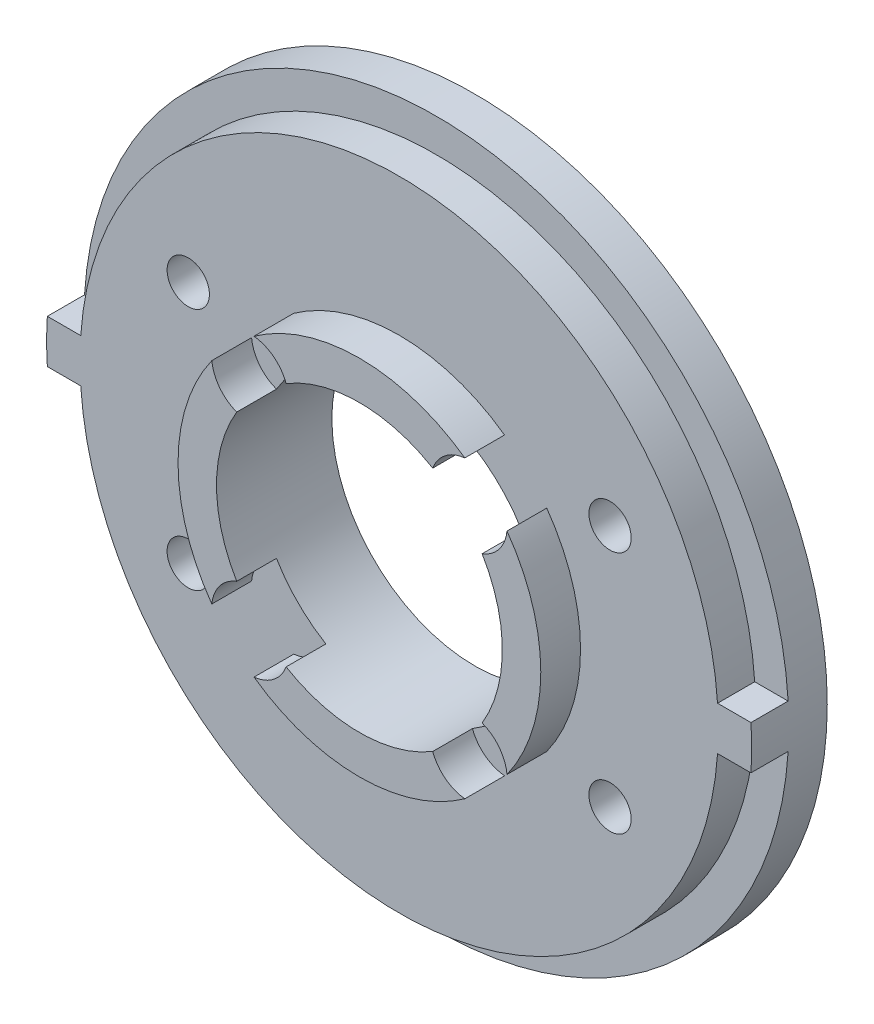
SolidWorks part; units mm, degrees
ref_plane "Front Plane" through (0, 0, 0) normal (0, 0, 1) x (1, 0, 0)
ref_plane "Top Plane" through (0, 0, 0) normal (0, 1, 0) x (1, 0, 0)
ref_plane "Right Plane" through (0, 0, 0) normal (1, 0, 0) x (0, 0, -1)
sketch "Sketch1" plane through (0, 0, 0) normal (0, 0, 1) x (1, 0, 0)
  circle A0 centre (0, 0) radius 11.15
  circle A1 centre (0, 0) radius 27.5
  dimension "D1" = 22.3
  dimension "D2" = 55
extrude "Boss-Extrude1" add sketch "Sketch1" along normal blind 9
sketch "Sketch2" plane through (0, 0, 0) normal (0, 0, 1) x (1, 0, 0)
  line L0 (-27.4474, 1.7) -> (-24.8402, 1.7)
  line L1 (-32.4957, 1.7) -> (38.4812, 1.7) construction
  line L2 (-32.4957, 1.7) -> (-32.4957, -1.7) construction
  line L3 (-32.4957, -1.7) -> (38.4812, -1.7) construction
  line L4 (38.4812, 1.7) -> (38.4812, -1.7) construction
  line L5 (24.8402, 1.7) -> (27.4474, 1.7)
  line L6 (27.4474, -1.7) -> (24.8419, -1.7)
  line L7 (-24.8419, -1.7) -> (-27.4474, -1.7)
  circle A0 centre (0, 0) radius 24.9 construction
  circle A1 centre (0, 0) radius 27.5 construction
  arc A2 (-27.4474, -1.7) -> (27.4474, -1.7) centre (0, 0) ccw
  circle A3 centre (0, 0) radius 27.5 construction
  arc A4 (-24.8419, -1.7) -> (24.8419, -1.7) centre (0, 0) ccw
  arc A5 (-24.8402, 1.7) -> (24.8402, 1.7) centre (0, 0) cw
  arc A6 (27.4474, 1.7) -> (-27.4474, 1.7) centre (0, 0) ccw
  point P8 (-32.4957, 0)
  dimension "D1" = 49.8
  dimension "D2" = 3.4
extrude "Cut-Extrude1" cut sketch "Sketch2" against normal blind 6 from surface at 9 starting at face at (27.5, 0, 9)
sketch "Sketch3" plane through (0, 0, 0) normal (0, 0, 1) x (1, 0, 0)
  circle A0 centre (0, 0) radius 14.15
  circle A1 centre (0, 0) radius 11.15 construction
  circle A2 centre (0, 0) radius 39.1859
  dimension "D1" = 3
extrude "Cut-Extrude2" cut sketch "Sketch3" against normal blind 3.1 from surface at 9 starting at face at (11.15, 0, 9)
sketch "Sketch4" plane through (0, 0, 0) normal (0, 0, 1) x (1, 0, 0)
  line L2 (0, 0) -> (-16.4545, 9.5) construction
  line L7 (0, 19) -> (0, -19) construction
  line L8 (-19, 0) -> (19, 0) construction
  circle A0 centre (0, 0) radius 19 construction
  circle A9 centre (-16.4545, 9.5) radius 1.65
  circle A13 centre (16.4545, 9.5) radius 1.65
  circle A14 centre (16.4545, -9.5) radius 1.65
  circle A15 centre (-16.4545, -9.5) radius 1.65
  point P18 (0, 0)
  point P38 (0, 0)
  dimension "D1" = 38
  dimension "D3" = 3.3
  dimension "D2" = 60
extrude "Cut-Extrude3" cut sketch "Sketch4" against normal through all from surface at 5.9 starting at face at (0, -0.0002, 5.9)
sketch "Sketch8" plane through (0, 0, 0) normal (0, 0, 1) x (1, 0, 0)
  circle A0 centre (-16.4545, 9.5) radius 3.3
  circle A1 centre (-16.4545, -9.5) radius 3.3
  circle A2 centre (16.4545, -9.5) radius 3.3
  circle A3 centre (16.4545, 9.5) radius 3.3
  circle A4 centre (16.4545, -9.5) radius 1.65 construction
  point P11 (0, 0)
  point P12 (16.4545, 9.5)
  dimension "D1" = 6.6
sketch "Sketch9" plane through (0, 0, 0) normal (0, 0, 1) x (1, 0, 0)
  line L1 (0, 33.1436) -> (0, 0) construction
  line L2 (0, 0) -> (-23.436, 23.436) construction
  circle A0 centre (0, 0) radius 33.1436 construction
  circle A1 centre (-8.531, 8.531) radius 3
  circle A2 centre (8.531, 8.531) radius 3
  circle A3 centre (8.531, -8.531) radius 3
  circle A4 centre (-8.531, -8.531) radius 3
  point P16 (0, 0)
  dimension "D2" = 6
  dimension "D1" = 45
  dimension "D3" = 4
extrude "Cut-Extrude9" cut sketch "Sketch9" against normal up to surface (3.1 mm away) from surface at 9 up to face at (-14.8045, -9.5, 5.9) starting at face at (11.15, 0, 9)
extrude "Cut-Extrude10" cut sketch "Sketch8" along normal blind 2.1 from surface at 0 starting at face at (-14.8045, -9.5, 0)
